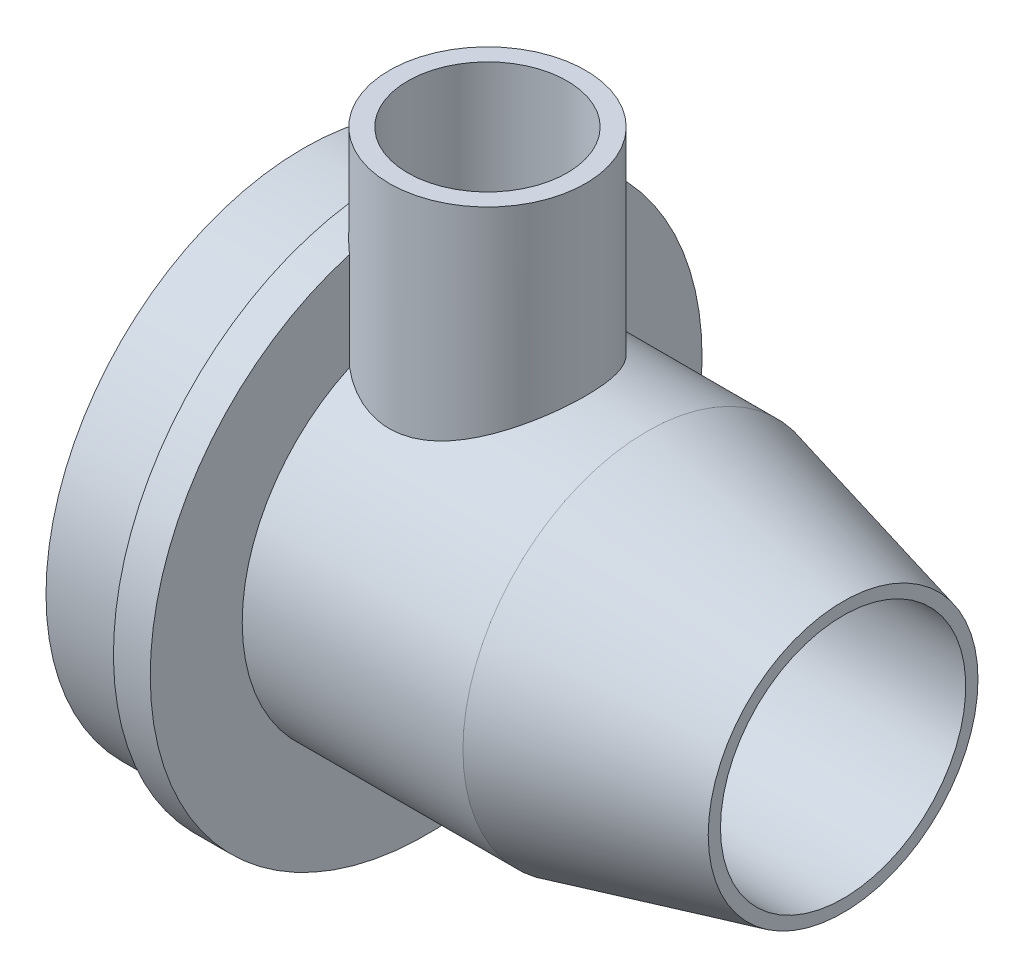
SolidWorks part; units mm, degrees
ref_plane "Plan de face" through (0, 0, 0) normal (0, 0, 1) x (1, 0, 0)
ref_plane "Plan de dessus" through (0, 0, 0) normal (0, 1, 0) x (1, 0, 0)
ref_plane "Plan de droite" through (0, 0, 0) normal (1, 0, 0) x (0, 0, -1)
sketch "Esquisse1" plane through (0, 0, 0) normal (0, 0, 1) x (1, 0, 0)
  line L0 (0, 0) -> (44, 0) construction
  line L1 (44, 0) -> (44, 10) construction
  line L2 (44, 10) -> (0, 10)
  line L3 (0, 10) -> (0, 21)
  line L4 (0, 21) -> (7, 21)
  line L5 (7, 21) -> (7, 22.5)
  line L6 (7, 22.5) -> (10, 22.5)
  line L7 (10, 22.5) -> (10, 15)
  line L8 (10, 15) -> (28, 15)
  line L9 (28, 15) -> (44, 11)
  line L10 (44, 11) -> (44, 10)
  dimension "D1" = 1
  dimension "D2" = 44
  dimension "D3" = 10
  dimension "D4" = 5
  dimension "D5" = 3
  dimension "D6" = 7
  dimension "D7" = 16
  dimension "D8" = 11
  dimension "D9" = 1.5
revolve "Révolution1" add sketch "Esquisse1" angle 360 about L0
ref_plane "Plan1" through (0, 30, 0) normal (0, 1, 0) x (1, 0, 0)
sketch "Esquisse2" plane through (0, 30, 0) normal (0, 1, 0) x (1, 0, 0)
  line L0 (0, 0) -> (15, 0) construction
  circle A0 centre (15, 0) radius 8
  dimension "D2" = 16
  dimension "D1" = 15
extrude "Boss.-Extru.1" add sketch "Esquisse2" against normal up to body separate body
sketch "Esquisse3" plane through (0, 30, 0) normal (0, 1, 0) x (1, 0, 0)
  line L0 (7, 0) -> (23, 0) construction
  line L1 (7, 21) -> (7, -21) construction
  circle A0 centre (15, 0) radius 8 construction
  circle A1 centre (15, 0) radius 6.5
  dimension "D1" = 13
extrude "Enlèv. mat.-Extru.1" cut sketch "Esquisse3" against normal up to body separate body
sketch "Esquisse4" plane through (0, 0, 0) normal (-1, 0, 0) x (0, 0, 1)
